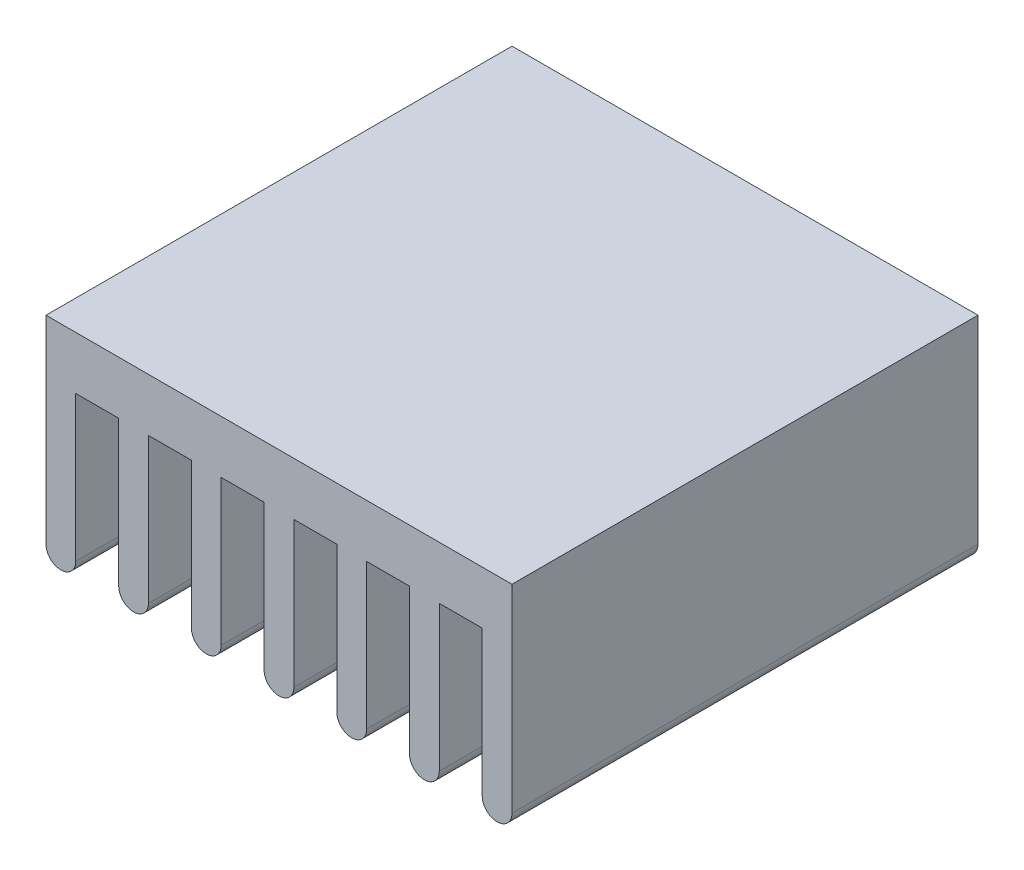
SolidWorks part; units mm, degrees
ref_plane "Plano frontal" through (0, 0, 0) normal (0, 0, 1) x (1, 0, 0)
ref_plane "Plano superior" through (0, 0, 0) normal (0, 1, 0) x (1, 0, 0)
ref_plane "Plano direito" through (0, 0, 0) normal (1, 0, 0) x (0, 0, -1)
sketch "Esboço1" plane through (0, 0, 0) normal (0, 0, 1) x (1, 0, 0)
  line L0 (0, 0) -> (14.0988, 0)
  line L1 (9.6988, -6) -> (9.6988, -1.6)
  line L2 (9.6988, -1.6) -> (10.9988, -1.6)
  line L3 (0, 0) -> (0, -6)
  line L4 (0.9, -1.6) -> (2.2, -1.6)
  line L5 (0.9, -1.6) -> (0.9, -6)
  line L6 (2.2, -1.6) -> (2.2, -6)
  line L7 (10.9988, -1.6) -> (10.9988, -6)
  line L8 (3.1, -6) -> (3.1, -1.6)
  line L9 (3.1, -1.6) -> (4.4, -1.6)
  line L10 (4.4, -1.6) -> (4.4, -6)
  line L11 (11.8988, -6) -> (11.8988, -1.6)
  line L12 (5.3, -6) -> (5.3, -1.6)
  line L13 (5.3, -1.6) -> (6.6, -1.6)
  line L14 (6.6, -1.6) -> (6.6, -6)
  line L15 (11.8988, -1.6) -> (13.1988, -1.6)
  line L16 (7.5, -6) -> (7.5, -1.6)
  line L17 (7.5, -1.6) -> (8.8, -1.6)
  line L18 (8.8, -1.6) -> (8.8, -6)
  line L19 (13.1988, -1.6) -> (13.1988, -6)
  line L20 (14.0988, -6) -> (14.0988, 0)
  arc A0 (0, -6) -> (0.9, -6) centre (0.45, -6) ccw
  arc A1 (2.2, -6) -> (3.1, -6) centre (2.65, -6) ccw
  arc A2 (4.4, -6) -> (5.3, -6) centre (4.85, -6) ccw
  arc A3 (6.6, -6) -> (7.5, -6) centre (7.05, -6) ccw
  arc A4 (8.8, -6) -> (9.6988, -6) centre (9.2494, -6) ccw
  arc A5 (10.9988, -6) -> (11.8988, -6) centre (11.4488, -6) ccw
  arc A6 (13.1988, -6) -> (14.0988, -6) centre (13.6488, -6) ccw
  point P12 (0, 0)
  point P36 (0, 0)
  dimension "D16" = 0.45
  dimension "D2" = 6
  dimension "D14" = 0.9
  dimension "D18" = 0.9
  dimension "D3" = 1.6
  dimension "D4" = 1.3
  dimension "D5" = 0.9
  dimension "D6" = 1.3
  dimension "D7" = 0.9
  dimension "D8" = 1.3
  dimension "D9" = 0.9
  dimension "D10" = 1.3
  dimension "D11" = 0.9
  dimension "D12" = 1.3
  dimension "D15" = 1.3
  dimension "D17" = 0.8988
extrude "Boss-Extrude1" add sketch "Esboço1" along normal blind 14.1
